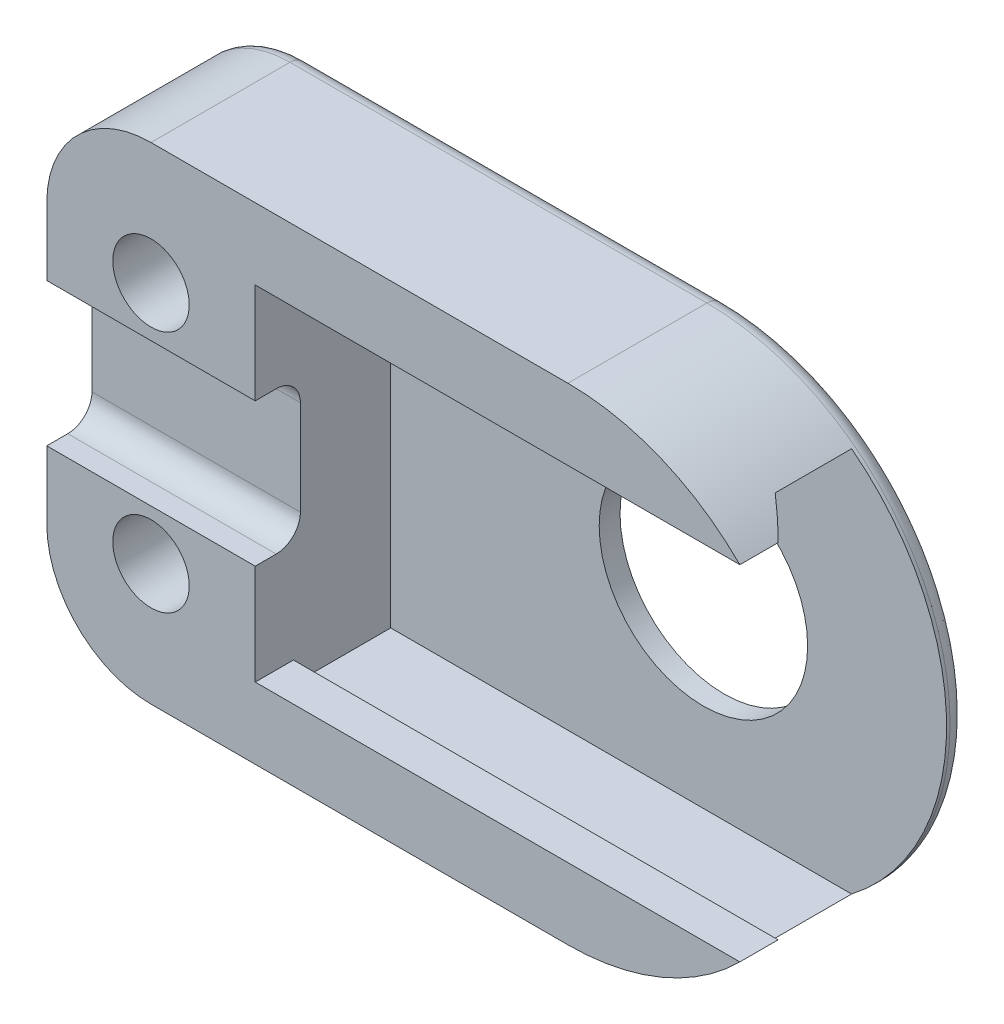
SolidWorks part; units mm, degrees
ref_plane "Front Plane" through (0, 0, 0) normal (0, 0, 1) x (1, 0, 0)
ref_plane "Top Plane" through (0, 0, 0) normal (0, 1, 0) x (1, 0, 0)
ref_plane "Right Plane" through (0, 0, 0) normal (1, 0, 0) x (0, 0, -1)
sketch "Sketch1" plane through (0, 0, 0) normal (0, 0, 1) x (1, 0, 0)
  line L0 (-1.7511, 0) -> (-50001.7511, 0) construction
  line L2 (-15, 7) -> (0, 7)
  line L3 (-15, 7) -> (-15, -7)
  line L4 (-15, -7) -> (0, -7)
  arc A1 (0, 7) -> (0, -7) centre (0, 0) cw
  circle A2 centre (-12, 3.5) radius 1.1
  circle A3 centre (-12, -3.5) radius 1.1
  dimension "D1" = 2.2
  dimension "D2" = 12
  dimension "D3" = 3
  dimension "D4" = 7
  dimension "D5" = 7
extrude "Boss-Extrude1" add sketch "Sketch1" along normal blind 4.5
sketch "Sketch2" plane through (0, 0, 0) normal (0, 0, -1) x (-1, 0, 0)
  circle A0 centre (0, 0) radius 3
  dimension "D1" = 6
extrude "Cut-Extrude2" cut sketch "Sketch2" against normal blind 10
sketch "Sketch7" plane through (-15, 0, 0) normal (-1, 0, 0) x (0, 0, 1)
  line L1 (0.6, 5.55) -> (0.6, -5.55)
  line L2 (0.6, 5.55) -> (2.8, 5.55)
  line L3 (2.8, 5.55) -> (3.4, 4.95)
  line L4 (3.4, 4.95) -> (4.5, 4.95)
  line L5 (4.5, 7) -> (4.5, -7) construction
  line L6 (0, 0) -> (8.4762, 0) construction
  line L7 (0.6, 0) -> (4.5, 0)
  line L8 (4.5, -4.95) -> (4.5, 4.95)
  line L9 (3.4, -4.95) -> (4.5, -4.95)
  line L10 (2.8, -5.55) -> (3.4, -4.95)
  line L11 (0.6, -5.55) -> (2.8, -5.55)
  point P10 (3.95, 4.95)
  line M10 (4.5, -7) -> (4.5, 7)
  dimension "D1" = 45
  dimension "D2" = 2.2
  dimension "D3" = 0.6
  dimension "D4" = 0.6
  dimension "D5" = 11.1
extrude "Cut-Extrude4" cut sketch "Sketch7" against normal through all from offset 6 contours L1 L7 L4 L3 L2 M10 | L1 L11 L10 L9 L7 M10 offset against normal yes
sketch "Sketch8" plane through (-15, 0, 0) normal (-1, 0, 0) x (0, 0, 1)
  line L0 (4.5, 7) -> (4.5, -7) construction
  line L1 (3.2, 1.3633) -> (3.2, -1.3633)
  line L2 (4.5, 2.06) -> (4.5, -2.06)
  line L3 (0, 0) -> (7.1519, 0) construction
  line L4 (4.5, 2.06) -> (3.8967, 2.06)
  line L5 (4.5, -2.06) -> (3.8967, -2.06)
  arc A0 (3.8967, 2.06) -> (3.2, 1.3633) centre (3.8967, 1.3633) ccw
  arc A1 (3.8967, -2.06) -> (3.2, -1.3633) centre (3.8967, -1.3633) cw
  point P8 (3.2, 0)
  point P18 (4.5, 0)
  dimension "D1" = 4.12
  dimension "D2" = 1.3
extrude "Cut-Extrude6" cut sketch "Sketch8" against normal through all
fillet "Fillet4" radius 3 2 edges at (-15, 7, 2.25) (-15, -7, 2.25)
fillet "Fillet1" radius 0.5 6 edges at (-14.1213, 6.1213, 0) (-6, 7, 0) (7, 0, 0) (-6, -7, 0) (-14.1213, -6.1213, 0) (-15, 0, 0)
sketch "Sketch5" plane through (0, 0, 0) normal (0, 0, 1) x (1, 0, 0)
  circle A0 centre (-12, 3.5) radius 1.75
  circle A1 centre (-12, -3.5) radius 1.75
  dimension "D1" = 3.5
extrude "Cut-Extrude5" cut sketch "Sketch5" along normal blind 1
